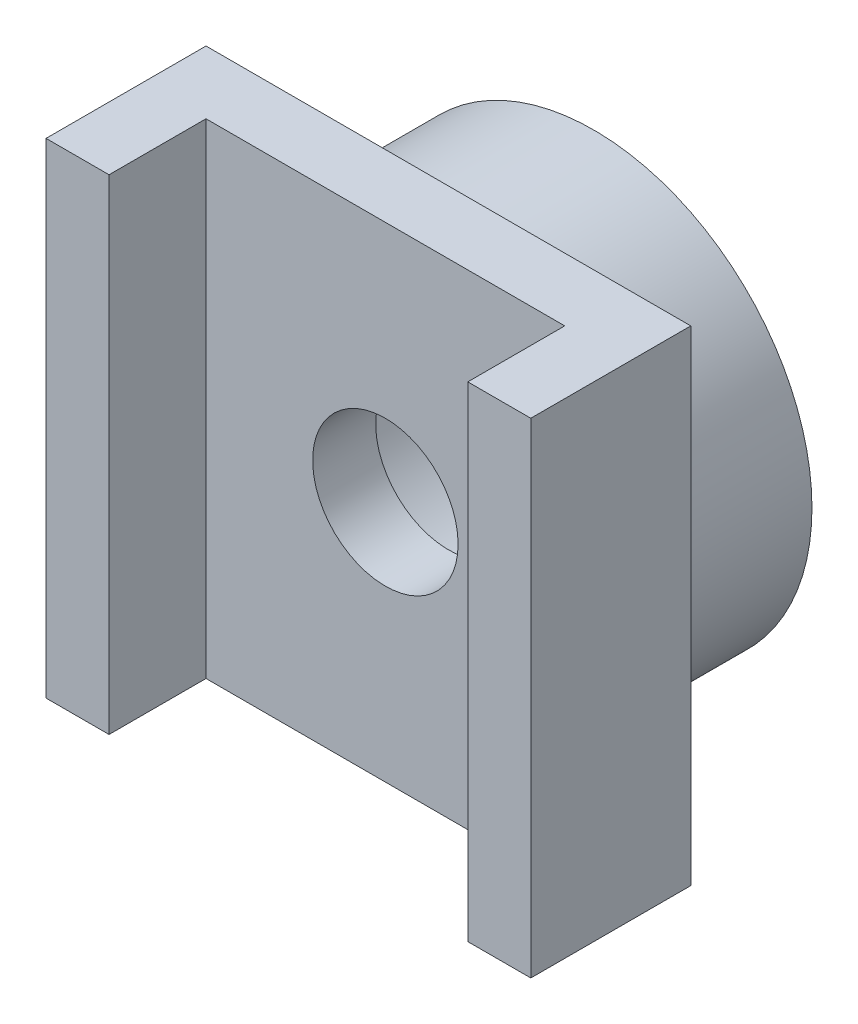
SolidWorks part; units mm, degrees
material "ABS"
ref_plane "Front Plane" through (0, 0, 0) normal (0, 0, 1) x (1, 0, 0)
ref_plane "Top Plane" through (0, 0, 0) normal (0, 1, 0) x (1, 0, 0)
ref_plane "Right Plane" through (0, 0, 0) normal (1, 0, 0) x (0, 0, -1)
sketch "Sketch1" plane through (0, 0, 0) normal (0, 0, 1) x (1, 0, 0)
  circle A0 centre (0, 0) radius 4.5
  circle A1 centre (0, 0) radius 2.85
  dimension "D1" = 9
  dimension "D2" = 5.7
extrude "Main Axis" add sketch "Sketch1" along normal blind 3
sketch "Sketch2" plane through (0, 0, 3) normal (0, 0, 1) x (1, 0, 0)
  line L5 (-5, -5) -> (5, -5)
  line L6 (-5, -5) -> (-5, 5)
  line L7 (-5, 5) -> (5, 5)
  line L8 (5, -5) -> (5, 5)
  line L9 (-5, -5) -> (5, 5) construction
  line L10 (-5, 5) -> (5, -5) construction
  circle A0 centre (0, 0) radius 1.5
  point P4 (0, 0)
  dimension "D2" = 3
  dimension "D1" = 10
extrude "Base of Rectagle" add sketch "Sketch2" along normal blind 1.3
sketch "Sketch3" plane through (0, 0, 4.3) normal (0, 0, 1) x (1, 0, 0)
  line L0 (-5, -5) -> (5, -5) construction
  line L1 (-5, 5) -> (-3.7, 5)
  line L2 (-5, 5) -> (-5, -5)
  line L3 (-5, -5) -> (-3.7, -5)
  line L4 (-3.7, 5) -> (-3.7, -5)
  line L6 (5, 5) -> (3.7, 5)
  line L7 (5, 5) -> (5, -5)
  line L8 (5, -5) -> (3.7, -5)
  line L9 (3.7, 5) -> (3.7, -5)
  dimension "D1" = 1.3
extrude "Pulley Support" add sketch "Sketch3" along normal blind 2
